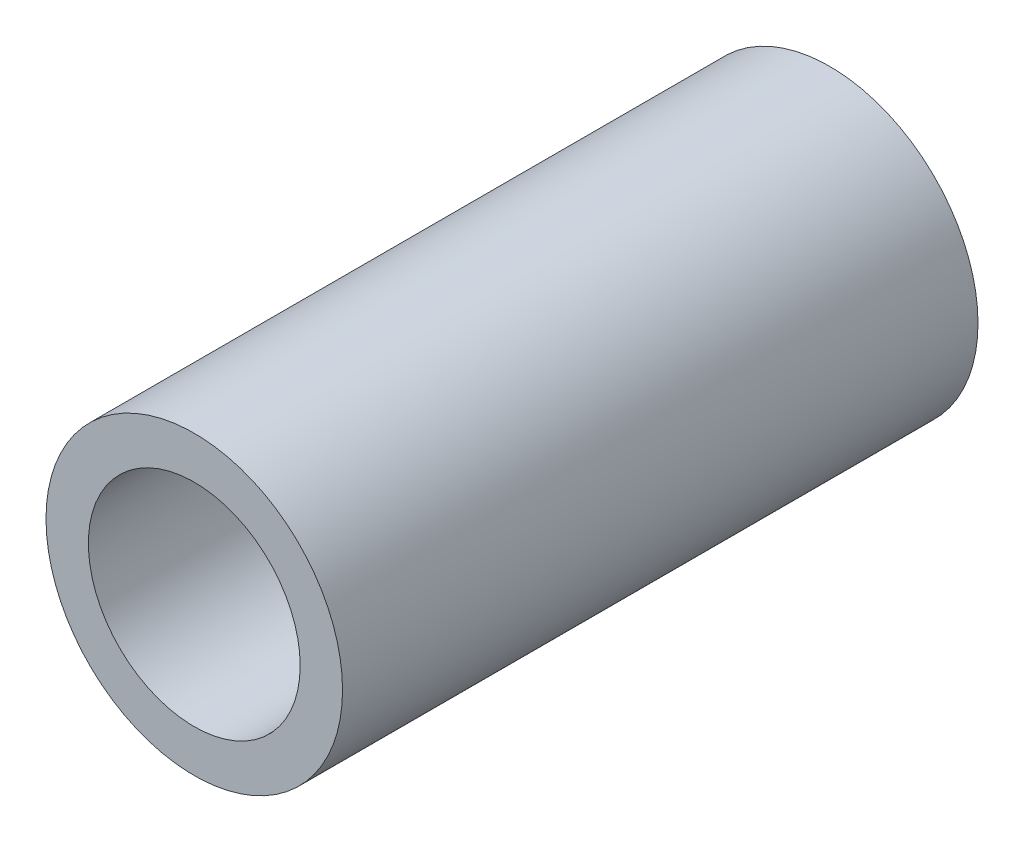
SolidWorks part; units mm, degrees
material "5052-H32"
ref_plane "Front Plane" through (0, 0, 0) normal (0, 0, 1) x (1, 0, 0)
ref_plane "Top Plane" through (0, 0, 0) normal (0, 1, 0) x (1, 0, 0)
ref_plane "Right Plane" through (0, 0, 0) normal (1, 0, 0) x (0, 0, -1)
sketch "Sketch1" plane through (0, 0, 0) normal (0, 0, 1) x (1, 0, 0)
  circle A0 centre (0, 0) radius 3.5
  circle A1 centre (0, 0) radius 2.5
  dimension "D1" = 5
  dimension "D2" = 7
extrude "Boss-Extrude1" add sketch "Sketch1" along normal blind 15
